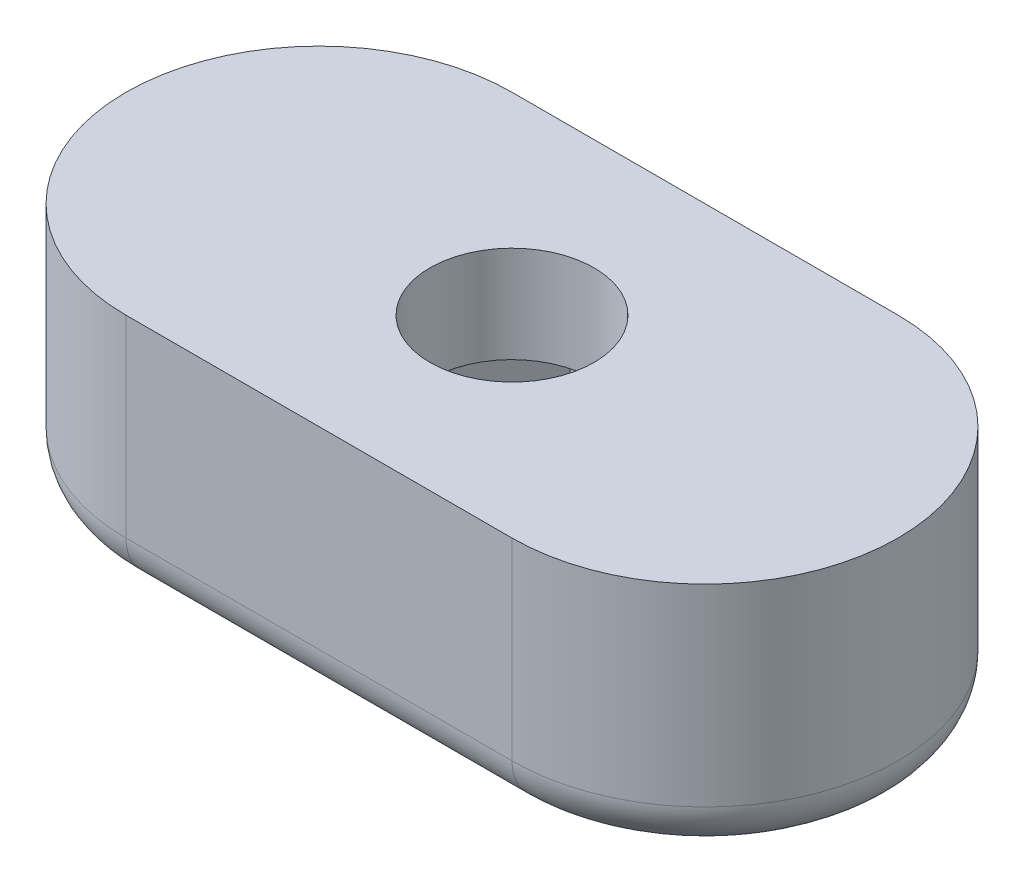
SolidWorks part; units mm, degrees
ref_plane "Plan de face" through (0, 0, 0) normal (0, 0, 1) x (1, 0, 0)
ref_plane "Plan de dessus" through (0, 0, 0) normal (0, 1, 0) x (1, 0, 0)
ref_plane "Plan de droite" through (0, 0, 0) normal (1, 0, 0) x (0, 0, -1)
sketch "Esquisse1" plane through (0, 0, 0) normal (0, 1, 0) x (1, 0, 0)
  line L0 (-1.6454, 2.85) -> (1.6454, 2.85)
  line L1 (1.6454, 2.85) -> (3.2909, 0)
  line L2 (3.2909, 0) -> (1.6454, -2.85)
  line L3 (1.6454, -2.85) -> (-1.6454, -2.85)
  line L4 (-1.6454, -2.85) -> (-3.2909, 0)
  line L5 (-3.2909, 0) -> (-1.6454, 2.85)
  line L6 (-3.2909, 0) -> (3.2909, 0) construction
  line L7 (-4, 0) -> (4, 0) construction
  line L8 (-4, 4) -> (4, 4)
  line L9 (-4, -4) -> (4, -4)
  arc A1 (-4, 4) -> (-4, -4) centre (-4, 0) ccw
  arc A2 (4, -4) -> (4, 4) centre (4, 0) ccw
  point P5 (0, 0)
  point P10 (0, 0)
  dimension "D3" = 4
  dimension "D1" = 5.7
  dimension "D2" = 120
  dimension "D4" = 8
extrude "Boss.-Extru.1" add sketch "Esquisse1" along normal blind 5
sketch "Esquisse2" plane through (0, 5, 0) normal (0, 1, 0) x (1, 0, 0)
  line L2 (-4, -4) -> (4, -4)
  line L3 (4, 4) -> (-4, 4)
  line L4 (-4, -4) -> (4, -4)
  line L5 (4, 4) -> (-4, 4)
  circle A0 centre (0, 0) radius 1.7
  arc A2 (-4, 4) -> (-4, -4) centre (-4, 0) ccw
  arc A3 (4, -4) -> (4, 4) centre (4, 0) ccw
  arc A4 (-4, 4) -> (-4, -4) centre (-4, 0) ccw
  arc A5 (4, -4) -> (4, 4) centre (4, 0) ccw
  dimension "D2" = 3.4
  dimension "D1" = 0
extrude "Boss.-Extru.2" add sketch "Esquisse2" against normal offset from surface (2 mm away) 3 up to face at (0, 0, 0)
fillet "Congé1" radius 1 4 edges at (0, 0, -4) (8, 0, 0) (0, 0, 4) (-8, 0, 0)
